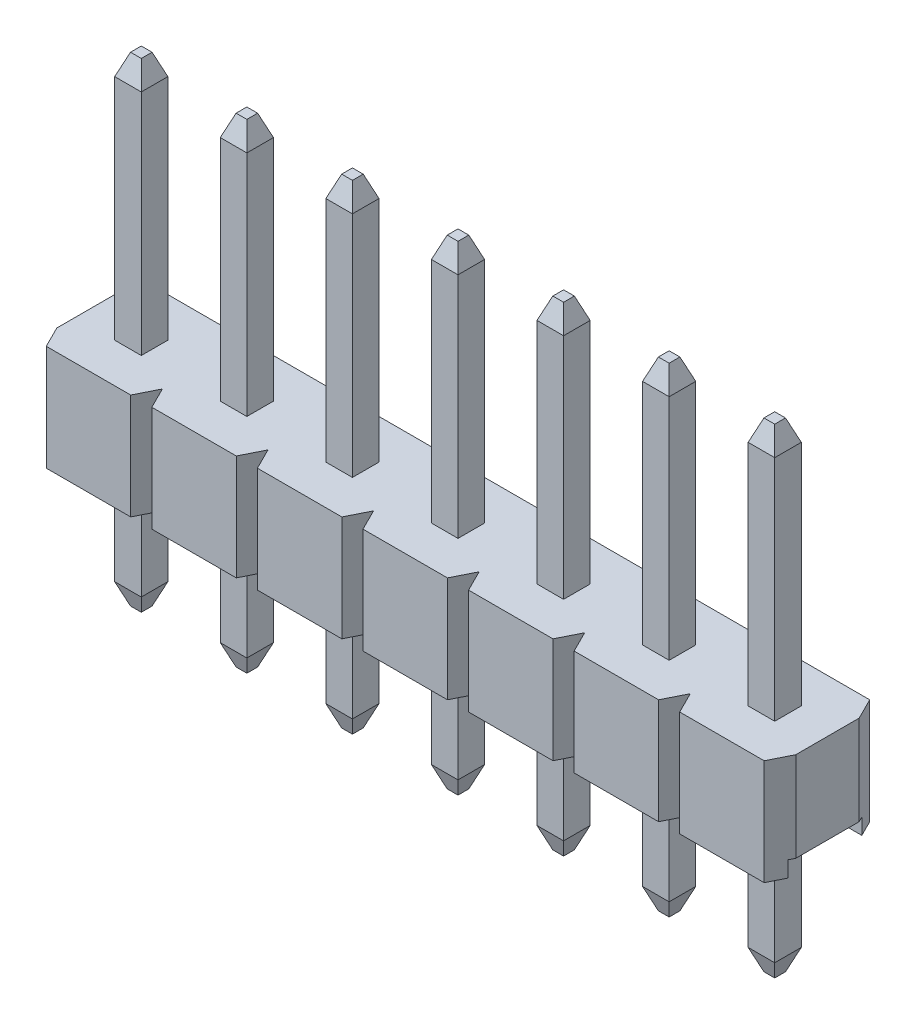
SolidWorks part; units mm, degrees
ref_plane "Front Plane" through (0, 0, 0) normal (0, 0, 1) x (1, 0, 0)
ref_plane "Top Plane" through (0, 0, 0) normal (0, 1, 0) x (1, 0, 0)
ref_plane "Right Plane" through (0, 0, 0) normal (1, 0, 0) x (0, 0, -1)
sketch "Sketch1" plane through (0, 0, 0) normal (0, 1, 0) x (1, 0, 0)
  line L1 (0, 0) -> (2.54, 0)
  line L2 (0, 0) -> (0, 2.54)
  line L3 (0, 2.54) -> (2.54, 2.54)
  line L4 (2.54, 0) -> (2.54, 2.54)
  dimension "D1" = 2.54
  dimension "D2" = 2.54
extrude "Main Body" add sketch "Sketch1" along normal blind 2.54
sketch "Sketch3" plane through (0, 0, 0) normal (-1, 0, 0) x (0, 0, 1)
  line L0 (-2.54, 0) -> (0, 0) construction
  line L1 (-2.159, 0) -> (-0.381, 0)
  line L2 (-2.159, 0) -> (-2.159, 0.381)
  line L3 (-2.159, 0.381) -> (-0.381, 0.381)
  line L4 (-0.381, 0) -> (-0.381, 0.381)
  line L5 (-2.54, 0) -> (-2.159, 0) construction
  line L6 (-0.381, 0) -> (0, 0) construction
  dimension "D1" = 0.381
extrude "Cut-Extrude1" cut sketch "Sketch3" against normal through all
sketch "Sketch4" plane through (0, 2.54, 0) normal (0, 1, 0) x (1, 0, 0)
  line L0 (0, 2.54) -> (0, 2.032)
  line L1 (0, 2.54) -> (0, 0) construction
  line L2 (0, 2.032) -> (0.254, 2.54)
  line L3 (2.54, 2.54) -> (0, 2.54) construction
  line L4 (0.254, 2.54) -> (0, 2.54)
  line L5 (2.54, 2.54) -> (2.286, 2.54)
  line L6 (2.286, 2.54) -> (2.54, 2.032)
  line L7 (2.54, 0) -> (2.54, 2.54) construction
  line L8 (2.54, 2.032) -> (2.54, 2.54)
  line L9 (2.54, 0) -> (2.286, 0)
  line L10 (0, 0) -> (2.54, 0) construction
  line L11 (2.286, 0) -> (2.54, 0.508)
  line L12 (2.54, 0.508) -> (2.54, 0)
  line L14 (0, 0) -> (0, 0.508)
  line L15 (0, 0.508) -> (0.254, 0)
  line L16 (0.254, 0) -> (0, 0)
  line M1 (0, 2.54) -> (0, 0)
  line M2 (0, 0) -> (2.54, 0)
  line M3 (2.54, 0) -> (2.54, 2.54)
  line M4 (2.54, 2.54) -> (0, 2.54)
  dimension "D1" = 0.254
  dimension "D2" = 0.508
extrude "Cut-Extrude2" cut sketch "Sketch4" against normal through all contours L2 M1 M4 | L6 M4 M3 | L15 M1 M2 | L9 L11 L12
pattern_linear "Body Pattern" count 7 spacing 2.54 along (-1, 0, 0) of "Main Body", "Cut-Extrude1", "Cut-Extrude2"
sketch "Sketch2" plane through (0, 2.54, 0) normal (0, 1, 0) x (1, 0, 0)
  line L0 (1.27, 2.54) -> (1.27, 1.59) construction
  line L1 (0.95, 0.95) -> (1.59, 0.95)
  line L2 (0.95, 0.95) -> (0.95, 1.59)
  line L3 (0.95, 1.59) -> (1.59, 1.59)
  line L4 (1.59, 0.95) -> (1.59, 1.59)
  line L6 (2.286, 2.54) -> (0.254, 2.54) construction
  line L8 (1.27, 0.95) -> (1.27, 0) construction
  line L9 (0.254, 0) -> (2.286, 0) construction
  dimension "D1" = 0.64
extrude "Pin" add sketch "Sketch2" along normal blind 6 and the other way offset from surface (5.54 mm away) 3 other way up to face at (1.27, 0, -0.1905)
chamfer "Chamfer1" distance 0.508 distance2 0.1905 4 edges at (0.95, 8.54, -1.27) (1.27, 8.54, -1.59) (1.59, 8.54, -1.27) (1.27, 8.54, -0.95)
chamfer "Chamfer2" distance 0.1905 distance2 0.508 4 edges at (1.27, -3, -1.59) (1.59, -3, -1.27) (1.27, -3, -0.95) (0.95, -3, -1.27)
pattern_linear "Pin Pattern" count 7 spacing 2.54 along (-1, 0, 0) of "Pin", "Chamfer1", "Chamfer2"
